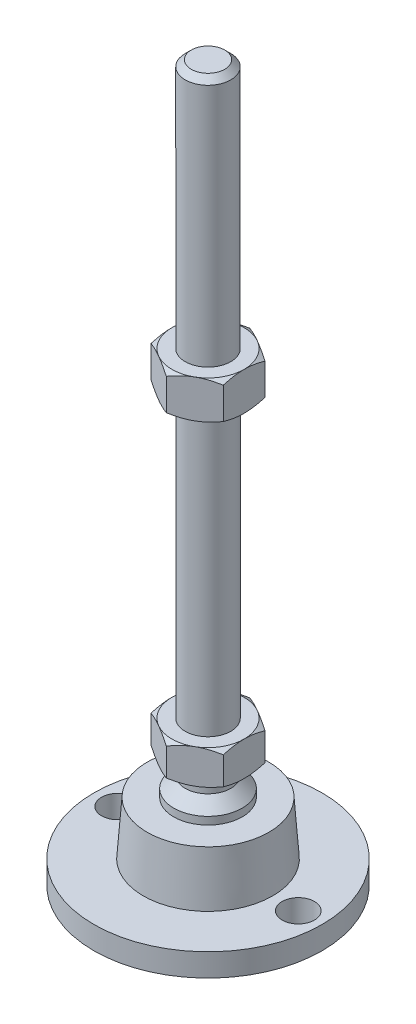
SolidWorks part; units mm, degrees
ref_plane "Спереди" through (0, 0, 0) normal (0, 0, 1) x (1, 0, 0)
ref_plane "Сверху" through (0, 0, 0) normal (0, 1, 0) x (1, 0, 0)
ref_plane "Справа" through (0, 0, 0) normal (1, 0, 0) x (0, 0, -1)
sketch "Эскиз1" plane through (0, 0, 0) normal (0, 0, 1) x (1, 0, 0)
  line L0 (0, 0) -> (-30, 0)
  line L3 (-30, 0) -> (-30, 6)
  line L12 (-6, 38) -> (-6, 186.4)
  line L13 (-6, 186.4) -> (-4.4, 188)
  line L14 (-4.4, 188) -> (0, 188)
  line L15 (0, 188) -> (0, 0) construction
  line L16 (-30, 6) -> (-17, 6)
  line L17 (0, 0) -> (0, 188)
  line L18 (0, 0) -> (0, -7.9595) construction
  line L19 (-6, 38) -> (-6, 29)
  line L21 (-9, 20) -> (-16, 20)
  line L22 (-17, 6) -> (-16, 20)
  line L23 (-9, 20) -> (-9, 22)
  line L24 (-9, 22) -> (-6, 25)
  line L25 (-6, 25) -> (-6, 29)
  line L26 (-6, 38) -> (0, 38) construction
  point P8 (-6, 112.2)
revolve "Повернуть1" add sketch "Эскиз1" angle 360 about L17
ref_plane "Плоскость2" through (0, 29, 0) normal (0, 1, 0) x (1, 0, 0)
sketch "Эскиз2" plane through (0, 29, 0) normal (0, 1, 0) x (1, 0, 0)
  line L1 (0, 10.9697) -> (-9.5, 5.4848)
  line L2 (-9.5, 5.4848) -> (-9.5, -5.4848)
  line L3 (-9.5, -5.4848) -> (0, -10.9697)
  line L4 (0, -10.9697) -> (9.5, -5.4848)
  line L5 (9.5, -5.4848) -> (9.5, 5.4848)
  line L6 (9.5, 5.4848) -> (0, 10.9697)
  circle A0 centre (0, 0) radius 9.5 construction
  dimension "D1" = 19
extrude "Бобышка-Вытянуть1" add sketch "Эскиз2" along normal up to vertex (9 mm away) up to point (-6, 38, 0)
ref_plane "Плоскость1" through (0, 112.2, 0) normal (0, 1, 0) x (1, 0, 0)
sketch "Эскиз3" plane through (0, 112.2, 0) normal (0, 1, 0) x (1, 0, 0)
  line L6 (9.5, 5.4848) -> (0, 10.9697)
  line L7 (0, 10.9697) -> (-9.5, 5.4848)
  line L8 (-9.5, 5.4848) -> (-9.5, -5.4848)
  line L9 (-9.5, -5.4848) -> (0, -10.9697)
  line L10 (0, -10.9697) -> (9.5, -5.4848)
  line L11 (9.5, -5.4848) -> (9.5, 5.4848)
  line L12 (9.5, 5.4848) -> (0, 10.9697)
  line L13 (0, 10.9697) -> (-9.5, 5.4848)
  line L14 (-9.5, 5.4848) -> (-9.5, -5.4848)
  line L15 (-9.5, -5.4848) -> (0, -10.9697)
  line L16 (0, -10.9697) -> (9.5, -5.4848)
  line L17 (9.5, -5.4848) -> (9.5, 5.4848)
  dimension "D1" = 0
extrude "Бобышка-Вытянуть2" add sketch "Эскиз3" along normal blind 10
sketch "Эскиз4" plane through (0, 0, 0) normal (0, 0, 1) x (1, 0, 0)
  line L0 (-9.5, 122.2) -> (-18.1603, 117.2)
  line L1 (-18.1603, 117.2) -> (-18.1603, 122.2)
  line L2 (-18.1603, 122.2) -> (-9.5, 122.2)
  line L3 (-18.1603, 117.2) -> (-9.5, 112.2)
  line L4 (50, 112.2) -> (-50, 112.2) construction
  line L5 (-9.5, 112.2) -> (-18.1603, 112.2)
  line L6 (-18.1603, 112.2) -> (-18.1603, 117.2)
  line L7 (-9.5, 122.2) -> (-9.5, 112.2) construction
  line L8 (-9.5, 38) -> (-17.2942, 38)
  line L9 (-17.2942, 38) -> (-17.2942, 33.5)
  line L10 (-17.2942, 33.5) -> (-9.5, 38)
  line L11 (-9.5, 29) -> (-17.2942, 33.5)
  line L12 (-17.2942, 33.5) -> (-17.2942, 29)
  line L13 (-17.2942, 29) -> (-9.5, 29)
  line L14 (0, 188) -> (0, 96.3793) construction
  line L15 (50, 29) -> (-50, 29) construction
  dimension "D1" = 30
  dimension "D2" = 30
revolve "Вырез-Повернуть2" cut sketch "Эскиз4" angle 360 about L14
sketch "Эскиз5" plane through (0, 6, 0) normal (0, 1, 0) x (1, 0, 0)
  line L0 (23.75, 0) -> (-23.75, 0) construction
  circle A0 centre (-23.75, 0) radius 4.25
  circle A1 centre (23.75, 0) radius 4.25
  circle A2 centre (0, 0) radius 30 construction
  dimension "D1" = 8.5
  dimension "D2" = 2
extrude "Вырез-Вытянуть1" cut sketch "Эскиз5" against normal through all
equation "\"D13@Эскиз1\"=\"D12@Эскиз1\"/2"
